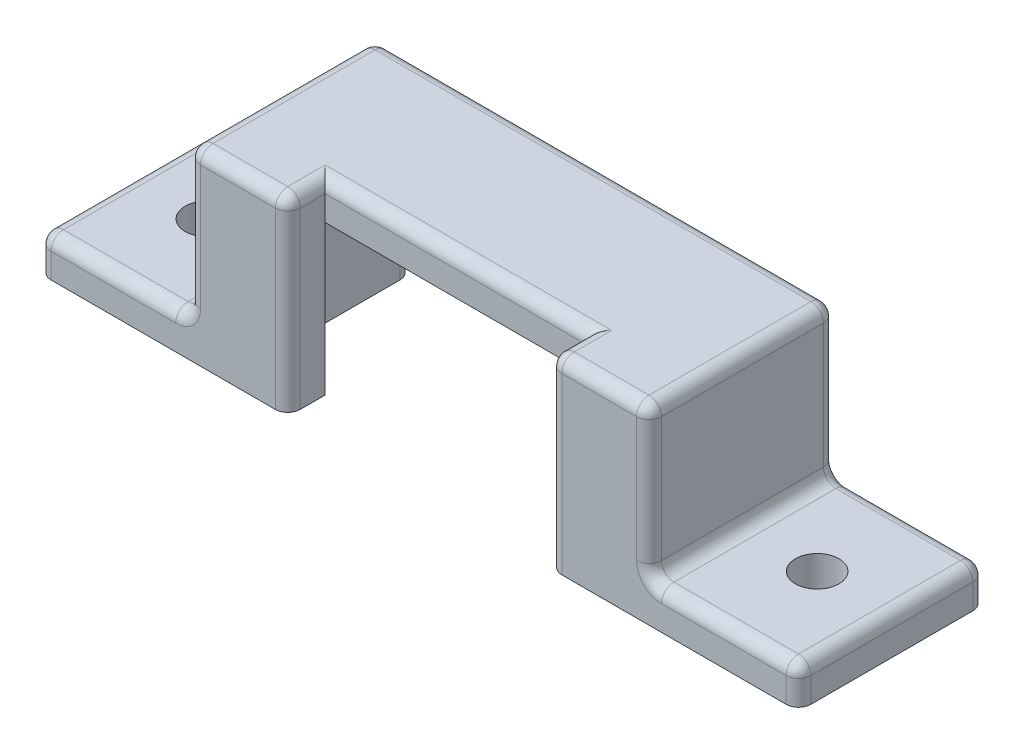
SolidWorks part; units mm, degrees
ref_plane "Front Plane" through (0, 0, 0) normal (0, 0, 1) x (1, 0, 0)
ref_plane "Top Plane" through (0, 0, 0) normal (0, 1, 0) x (1, 0, 0)
ref_plane "Right Plane" through (0, 0, 0) normal (1, 0, 0) x (0, 0, -1)
sketch "Sketch1" plane through (0, 0, 0) normal (0, 0, 1) x (1, 0, 0)
  line L0 (0, 0) -> (0, 17.3508) construction
  line L1 (-0.4721, 0) -> (-4.9574, 0) construction
  line L2 (-30.5, 3) -> (-18.5, 3)
  line L3 (-30.5, 3) -> (-30.5, 0)
  line L4 (-30.5, 0) -> (-15.5, 0)
  line L7 (-18.5, 3) -> (-18.5, 15)
  line L9 (-15.5, 0) -> (-15.5, 12)
  line L16 (0.4721, 0) -> (4.9574, 0) construction
  line L17 (-15.5, 12) -> (15.5, 12)
  line L19 (-18.5, 15) -> (18.5, 15)
  line L21 (15.5, 0) -> (15.5, 12)
  line L22 (18.5, 3) -> (18.5, 15)
  line L23 (30.5, 0) -> (15.5, 0)
  line L24 (30.5, 3) -> (30.5, 0)
  line L25 (30.5, 3) -> (18.5, 3)
  point P4 (0, 0)
  dimension "D1" = 12
  dimension "D2" = 3
  dimension "D3" = 3
  dimension "D4" = 12
  dimension "D5" = 15.5
  dimension "D6" = 3
extrude "Boss-Extrude1" add sketch "Sketch1" against normal blind 12
sketch "Sketch2" plane through (0, 0, 0) normal (0, 0, 1) x (1, 0, 0)
  line L0 (0, 0) -> (0, 22.4931) construction
  line L1 (-18.5, 15) -> (-10.5, 15)
  line L2 (-18.5, 15) -> (-18.5, 3)
  line L4 (-10.5, 15) -> (-10.5, 0)
  line L5 (-30.5, 3) -> (-18.5, 3)
  line L6 (-30.5, 3) -> (-30.5, 0)
  line L7 (-30.5, 0) -> (-10.5, 0)
  line L9 (30.5, 0) -> (10.5, 0)
  line L10 (30.5, 3) -> (30.5, 0)
  line L11 (30.5, 3) -> (18.5, 3)
  line L12 (10.5, 15) -> (10.5, 0)
  line L13 (18.5, 15) -> (18.5, 3)
  line L14 (18.5, 15) -> (10.5, 15)
  dimension "D1" = 8
  dimension "D2" = 3
extrude "Boss-Extrude2" add sketch "Sketch2" along normal blind 3
fillet "Fillet1" radius 1 28 edges at (-18.5, 9, -12) (-18.5, 9, 3) (18.5, 9, -12) (18.5, 9, 3) (-24.5, 3, -12) (-18.5, 3, -4.5) (-24.5, 3, 3) (-30.5, 3, -4.5) (-10.5, 15, 1.5) (-14.5, 15, 3) (-18.5, 15, -4.5) (0, 15, -12) (18.5, 15, -4.5) (14.5, 15, 3) (10.5, 15, 1.5) (0, 15, 0) (24.5, 3, -12) (30.5, 3, -4.5) (24.5, 3, 3) (18.5, 3, -4.5) (-15.5, 6, -12) (15.5, 6, -12) (-30.5, 1.5, -12) (-30.5, 1.5, 3) (30.5, 1.5, -12) (30.5, 1.5, 3) (10.5, 7.5, 3) (-10.5, 7.5, 3)
sketch "Sketch3" plane through (0, 3, 0) normal (0, 1, 0) x (1, 0, 0)
  line L0 (0, 0) -> (0, 23.761) construction
  line L1 (-30.5, 4.5) -> (-14.4084, 4.5) construction
  line L2 (-30.5, 12) -> (-30.5, -3) construction
  line L3 (-24.5, 12) -> (-24.5, -3) construction
  line L4 (-18.5, 12) -> (-30.5, 12) construction
  line L5 (-18.5, -3) -> (-30.5, -3) construction
  circle A0 centre (-24.5, 4.5) radius 1.75
  circle A1 centre (24.5, 4.5) radius 1.75
extrude "Cut-Extrude2" cut sketch "Sketch3" against normal blind 3
